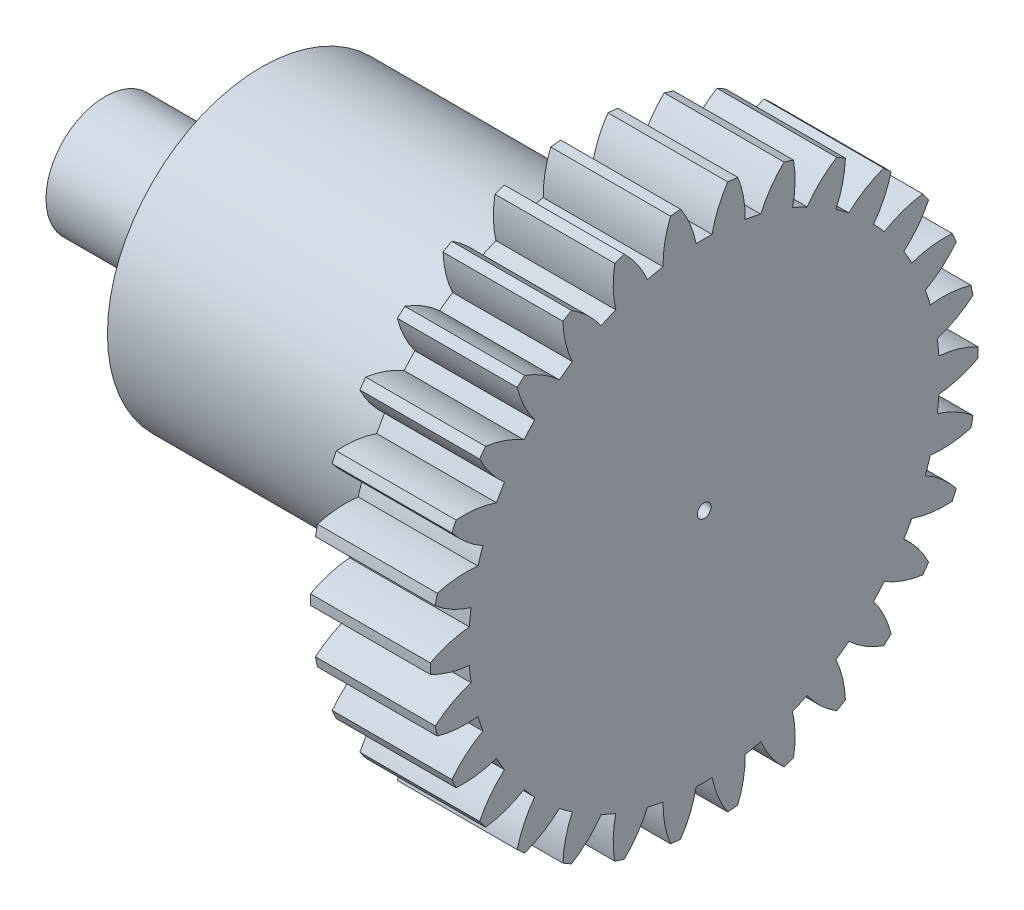
SolidWorks part; units mm, degrees
ref_plane "Plane1" through (0, 0, 0) normal (0, 0, 1) x (1, 0, 0)
ref_plane "Plane2" through (0, 0, 0) normal (0, 1, 0) x (1, 0, 0)
ref_plane "Plane3" through (0, 0, 0) normal (1, 0, 0) x (0, 0, -1)
sketch "HoldingSke" plane through (0, 0, 0) normal (0, 1, 0) x (1, 0, 0)
  line L0 (0, 0) -> (0.866, -0.5)
  line L1 (-15, 0) -> (100, 0) construction
  line L2 (0, 0) -> (-2.1039, 2.3779)
  line L3 (0, 0) -> (-11.863, 4.5341)
  line L4 (0, 0) -> (7.479, 4.318)
  line L5 (0, 0) -> (-46.8476, -17.4728)
  line L6 (0, 0) -> (-5.8027, -3.9151)
  line L7 (-2.1039, 2.3779) -> (8.6586, 51.2059)
  line L8 (-76.2, 54.61) -> (-76.1, 54.61)
  line L9 (-71.009, 38.7566) -> (-53.1078, 45.2721)
  line L10 (-76.2, 71.12) -> (104.1128, 71.12)
  line L11 (0, 0) -> (-7, 0)
  line L12 (-76.2, 101.6) -> (-76.162, 101.6)
  line L13 (24.9733, 27.94) -> (52.9518, 28.4284)
  line L14 (24.9733, 27.94) -> (24.9743, 27.94)
  line L15 (24.9733, 27.94) -> (100.4006, 29.5858)
  line L16 (-63.627, -1) -> (-12.827, -1)
  circle A0 centre (0, 0) radius 0.4
  circle A1 centre (0, 0) radius 13.749
  circle A2 centre (0, 0) radius 37.5
  circle A3 centre (0, 0) radius 0.4
  dimension "MHD" = 27.498
  dimension "Hub_dia" = 75
  dimension "Bore" = 0.8
  dimension "MBD" = 0.8
  dimension "Num_teeth" = 30
  dimension "Pitch" = 1
  dimension "Overall_len" = 50
  dimension "Show_teeth" = 30
  dimension "Thickness" = 7
  dimension "OAL" = 50.0001
  dimension "T_dim" = 0.1
  dimension "Ap" = 20
  dimension "H" = 19.05
  dimension "Pitch_radius" = 180.3128
  dimension "Width" = 7
  dimension "Backlash" = 0.038
  dimension "Addendum_fac" = 1
  dimension "Dedendum_fac" = 1.25
  dimension "Clearance_fac" = 0.25
  dimension "Dedendum_add" = 0.001
  dimension "Module" = 1
sketch "BasProSke" plane through (0, 0, 0) normal (0, 1, 0) x (1, 0, 0)
  line L0 (-10, 0) -> (60, 0) construction
  line L1 (0, 0) -> (0, 16)
  line L2 (0, 0) -> (7, 0)
  line L3 (7, 0) -> (7, 16)
  line L4 (7, 16) -> (0, 16)
  dimension "Thickness" = 7
  dimension "Diameter" = 32
revolve "Base-Revolve" add sketch "BasProSke" angle 360 about L0
sketch "TooCutSke" plane through (0, 0, 0) normal (1, 0, 0) x (0, 0, -1)
  line L1 (0, 0) -> (0, 107) construction
  line L2 (0, 0) -> (-0.8515, 14.9758) construction
  line L3 (0, 0) -> (-3.1323, 29.8014) construction
  line L4 (-0.8515, 14.9758) -> (-1.5661, 14.9007) construction
  arc A0 (0.4664, 13.7411) -> (-0.4664, 13.7411) centre (0, 0) ccw
  arc A1 (1.3975, 15.9644) -> (-1.3975, 15.9644) centre (0, 0) ccw
  circle A2 centre (0, 0) radius 15 construction
  circle A3 centre (0, 0) radius 14.0954 construction
  arc A4 (-0.4664, 13.7411) -> (-1.3975, 15.9644) centre (-6.3534, 12.5823) ccw
  arc A5 (1.3975, 15.9644) -> (0.4664, 13.7411) centre (6.3534, 12.5823) ccw
  dimension "Root_dia" = 27.498
  dimension "Overcut_dia" = 32.0508
  dimension "Pitch_dia" = 30
  dimension "Base_dia" = 28.1908
  dimension "Flank_rad" = 6
  dimension "Half_ang" = 6
  dimension "Half_CT" = 0.7185
extrude "ToothCut" cut sketch "TooCutSke" along normal through all
fillet "Breaks" [suppressed] radius 0.02
fillet "RootFillets" [suppressed] radius 0.251
pattern_circular "TeethCuts" count 30 every 12 about axis through (-10, 0, 0) along (1, 0, 0) of "ToothCut", "RootFillets", "Breaks"
sketch "HubNeaOneSke" plane through (0, 0, 0) normal (-1, 0, 0) x (0, 0, 1)
  circle A0 centre (0, 0) radius 13.749
  dimension "Diameter" = 27.498
extrude "HubNearOne" [suppressed] add sketch "HubNeaOneSke" along normal blind 43.0001
sketch "HubNeaBotSke" plane through (0, 0, 0) normal (-1, 0, 0) x (0, 0, 1)
  circle A0 centre (0, 0) radius 13.749
  dimension "Diameter" = 27.498
extrude "HubNearBoth" [suppressed] add sketch "HubNeaBotSke" along normal blind 21.5
ref_plane "FarPln" through (7, 0, 0) normal (1, 0, 0) x (0, 0, -1)
sketch "HubFarSke" plane through (7, 0, 0) normal (1, 0, 0) x (0, 0, -1)
  circle A0 centre (0, 0) radius 13.749
  dimension "Diameter" = 27.498
extrude "HubFar" [suppressed] add sketch "HubFarSke" along normal blind 21.5
sketch "BorSke" plane through (0, 0, 0) normal (1, 0, 0) x (0, 0, -1)
  circle A0 centre (0, 0) radius 0.4
  dimension "Diameter" = 0.8
extrude "Bore" cut sketch "BorSke" along normal mid plane 100.0001
sketch "KeySke" plane through (0, 0, 0) normal (1, 0, 0) x (0, 0, -1)
  line L0 (-0.05, 0) -> (-0.05, 0.5)
  line L1 (-0.05, 0.5) -> (0.05, 0.5)
  line L2 (0.05, 0.5) -> (0.05, 0)
  line L3 (0, 0) -> (0, 34) construction
  line L4 (-0.05, 0) -> (0.05, 0)
  dimension "Offset" = 0.5
  dimension "Width" = 0.1
extrude "Keyway" [suppressed] cut sketch "KeySke" along normal mid plane 100.0001
pattern_circular "Keyway2" [suppressed] count 2 every 90 about axis through (-10, 0, 0) along (1, 0, 0)
sketch "Sketch1" plane through (0, 0, 0) normal (-1, 0, 0) x (0, 0, 1)
  circle A0 centre (-0.1383, 0.3753) radius 9
  circle A1 centre (0, 0) radius 0.4 construction
  dimension "D1" = 18
extrude "Boss-Extrude1" add sketch "Sketch1" along normal blind 19
sketch "Sketch2" plane through (-19, 0, 0) normal (-1, 0, 0) x (0, 0, 1)
  circle A0 centre (0, 0) radius 3.45
  dimension "D1" = 6.9
extrude "Boss-Extrude2" add sketch "Sketch2" along normal blind 9
equation "' \"Module@HoldingSke\" = 6.35"
equation "' \"Num_teeth@HoldingSke\" = 12"
equation "' \"Ap@HoldingSke\" =  20"
equation "' \"Ap@HoldingSke\" = 20"
equation "' \"Width@HoldingSke\" = 0.5 * 25.4"
equation "' \"Hub_dia@HoldingSke\"= 1 * 25.4"
equation "' \"Hub_dia@HoldingSke\" = 1 * 25.4"
equation "' \"Overall_len@HoldingSke\" = 1.0 * 25.4"
equation "' \"Bore@HoldingSke\" = 0.75 * 25.4"
equation "' \"T_dim@HoldingSke\" = 0.1 * 25.4"
equation "' \"Width@KeySke\" = 0.25 * 25.4"
equation "' \"Show_teeth@HoldingSke\" = 13"
equation "' \"Backlash@HoldingSke\" = 0.009 * 25.4"
equation "' \"Addendum_fac@HoldingSke\" = 1.0"
equation "' \"Dedendum_fac@HoldingSke\" = 1.25"
equation "' \"Dedendum_add@HoldingSke\" = 0.00005 * 25.4"
equation "' \"Clearance_fac@HoldingSke\" = 0.25"
equation "\"Pitch@HoldingSke\" = 1 / \"Module@HoldingSke\""
equation "\"Overcut_dia@TooCutSke\" = (\"Num_teeth@HoldingSke\" + 2 * \"Addendum_fac@HoldingSke\") / \"Pitch@HoldingSke\" + 0.002 * 25.4"
equation "\"Pitch_dia@TooCutSke\" = \"Num_teeth@HoldingSke\" / \"Pitch@HoldingSke\""
equation "\"Base_dia@TooCutSke\" = \"Num_teeth@HoldingSke\" / \"Pitch@HoldingSke\" * cos((\"Ap@HoldingSke\"  * 3.14159265 / 180))"
equation "\"Root_dia@TooCutSke\" = (\"Num_teeth@HoldingSke\" + 2) / \"Pitch@HoldingSke\" - 2 * (\"Addendum_fac@HoldingSke\" + \"Dedendum_fac@HoldingSke\") / \"Pitch@HoldingSke\" - \"Dedendum_add@HoldingSke\" * 2"
equation "\"Half_ang@TooCutSke\" = 180 / \"Num_teeth@HoldingSke\""
equation "\"Half_CT@TooCutSke\" = \"Num_teeth@HoldingSke\" / \"Pitch@HoldingSke\" * sin((3.14159265 / 2 / \"Num_teeth@HoldingSke\")) / 2 - 7 * \"Backlash@HoldingSke\" / 4"
equation "\"Flank_rad@TooCutSke\" = \"Num_teeth@HoldingSke\" / \"Pitch@HoldingSke\" / 5"
equation "\"Radius@RootFillets\" = \"Clearance_fac@HoldingSke\" / \"Pitch@HoldingSke\" + \"Dedendum_add@HoldingSke\""
equation "\"Break_rad@Breaks\" = 0.02 / \"Pitch@HoldingSke\""
equation "\"Thickness@HoldingSke\" = \"Width@HoldingSke\""
equation "\"OAL@HoldingSke\" = \"Thickness@HoldingSke\""
equation "\"MHD@HoldingSke\" = (\"Num_teeth@HoldingSke\" + 2) / \"Pitch@HoldingSke\" - 2 * (\"Addendum_fac@HoldingSke\" + \"Dedendum_fac@HoldingSke\")  / \"Pitch@HoldingSke\" - \"Dedendum_add@HoldingSke\" * 2"
equation "\"MBD@HoldingSke\" = (\"Num_teeth@HoldingSke\" + 2) / \"Pitch@HoldingSke\" - 2 * (\"Addendum_fac@HoldingSke\" + \"Dedendum_fac@HoldingSke\")  / \"Pitch@HoldingSke\" - \"Dedendum_add@HoldingSke\" * 2 - 0.002 * 25.4"
equation "\"MHD@HoldingSke\" = ((sgn( \"MHD@HoldingSke\" - \"Hub_dia@HoldingSke\" )-1)*( \"MHD@HoldingSke\" - \"Hub_dia@HoldingSke\" ))/-2+ \"Hub_dia@HoldingSke\""
equation "\"MBD@HoldingSke\" = ((sgn( \"MBD@HoldingSke\" - \"Bore@HoldingSke\" )-1)*( \"MBD@HoldingSke\" - \"Bore@HoldingSke\" ))/-2+ \"Bore@HoldingSke\""
equation "\"OAL@HoldingSke\" = ((sgn( \"OAL@HoldingSke\" - \"Overall_len@HoldingSke\" )+1)*( \"OAL@HoldingSke\" - \"Overall_len@HoldingSke\" ))/2 + \"Overall_len@HoldingSke\" + 0.000002 * 25.4"
equation "\"Num_teeth@TeethCuts\" = int( \"Show_teeth@HoldingSke\" ) + 1"
equation "\"Num_teeth@TeethCuts\" = ((sgn( \"Num_teeth@TeethCuts\" - \"Num_teeth@HoldingSke\" )-1)*( \"Num_teeth@TeethCuts\" - \"Num_teeth@HoldingSke\" ))/-2+ \"Num_teeth@HoldingSke\""
equation "\"Num_teeth@TeethCuts\" = ((sgn( \"Num_teeth@TeethCuts\" - 2.0)+1)*( \"Num_teeth@TeethCuts\" - 2.0))/2 +2.0"
equation "\"Angle@TeethCuts\" = 360.0 / \"Num_teeth@HoldingSke\""
equation "\"Diameter@BasProSke\" = (\"Num_teeth@HoldingSke\" + 2 * \"Addendum_fac@HoldingSke\") / \"Pitch@HoldingSke\""
equation "\"Thickness@BasProSke\"  = \"Thickness@HoldingSke\""
equation "' \"Fillet_rad@BasProSke\" =  \"Thickness@HoldingSke\" * 0.05"
equation "' \"Fillet_rad@BasProSke\" = \"Thickness@HoldingSke\" * 0.05"
equation "\"MHD@HoldingSke\" = ((sgn( \"MHD@HoldingSke\" - \"Root_dia@TooCutSke\" )-1)*( \"MHD@HoldingSke\" - \"Root_dia@TooCutSke\" ))/-2+ \"Root_dia@TooCutSke\""
equation "\"Diameter@HubNeaOneSke\" = \"MHD@HoldingSke\""
equation "\"Length@HubNearOne\" = \"OAL@HoldingSke\" - \"Thickness@BasProSke\""
equation "\"Diameter@HubNeaBotSke\" = \"MHD@HoldingSke\""
equation "\"Length@HubNearBoth\" = ( \"OAL@HoldingSke\" - \"Thickness@BasProSke\" ) / 2.0"
equation "\"Thickness@FarPln\" = \"Thickness@BasProSke\""
equation "\"Diameter@HubFarSke\" = \"MHD@HoldingSke\""
equation "\"Length@HubFar\" = ( \"OAL@HoldingSke\" - \"Thickness@BasProSke\" ) / 2.0"
equation "\"Diameter@BorSke\" = \"MBD@HoldingSke\""
equation "\"D1@Bore\" = \"OAL@HoldingSke\" * 2.0"
equation "\"D1@Keyway\" = \"OAL@HoldingSke\" * 2.0"
equation "\"Offset@KeySke\" = \"T_dim@HoldingSke\" + \"MBD@HoldingSke\" / 2.0"
